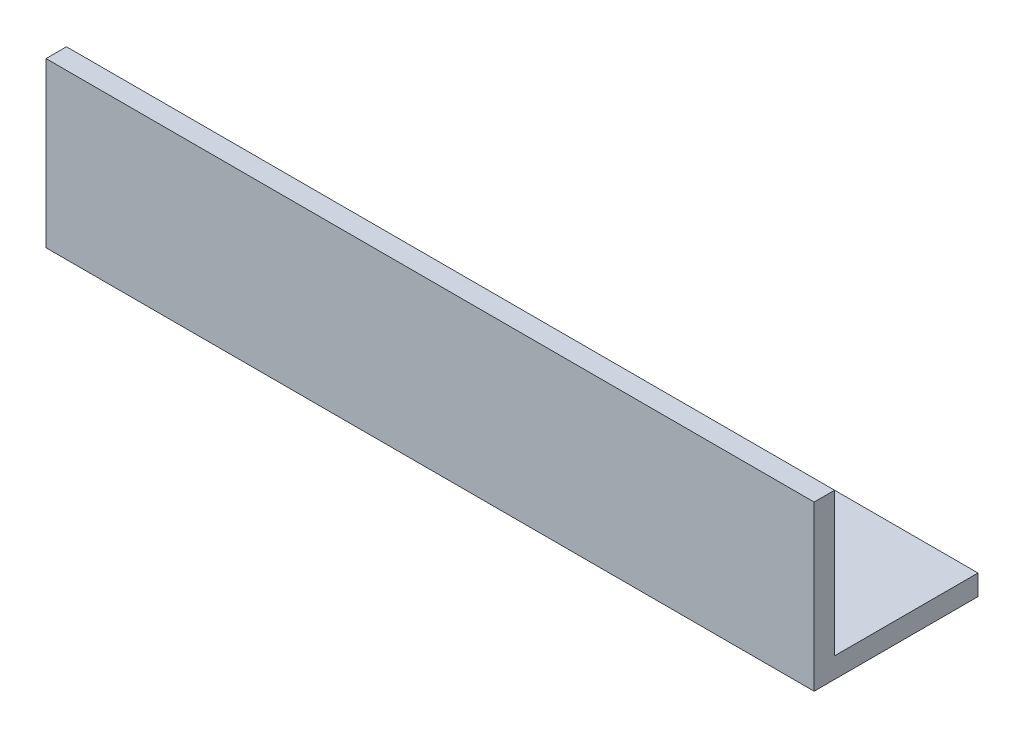
SolidWorks part; units mm, degrees
ref_plane "Спереди" through (0, 0, 0) normal (0, 0, 1) x (1, 0, 0)
ref_plane "Сверху" through (0, 0, 0) normal (0, 1, 0) x (1, 0, 0)
ref_plane "Справа" through (0, 0, 0) normal (1, 0, 0) x (0, 0, -1)
sketch "Эскиз1" plane through (0, 0, 0) normal (1, 0, 0) x (0, 0, -1)
  line L0 (0, 0) -> (0, 32)
  line L1 (0, 0) -> (32, 0)
extrude "Вытянуть-Тонкостенный1" add sketch "Эскиз1" along normal blind 150 thin
sketch "Эскиз2" plane through (0, 0, 0) normal (0, -1, 0) x (1, 0, 0)
  line L0 (75, -35.2679) -> (75, 2.5217) construction
  circle A0 centre (130, -13) radius 5
  circle A1 centre (100, -13) radius 5
  circle A2 centre (50, -13) radius 5
  circle A3 centre (20, -13) radius 5
  dimension "D1" = 2
extrude "Вырез-Вытянуть1" cut sketch "Эскиз2" against normal through all
